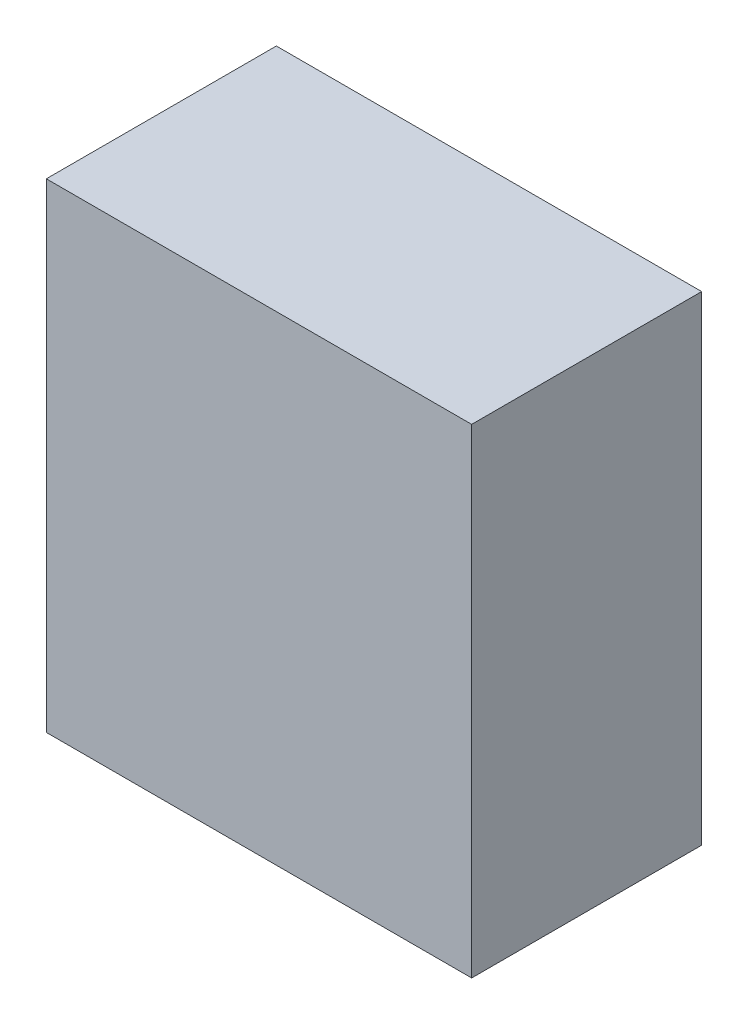
SolidWorks part; units mm, degrees
ref_plane "Front Plane" through (0, 0, 0) normal (0, 0, 1) x (1, 0, 0)
ref_plane "Top Plane" through (0, 0, 0) normal (0, 1, 0) x (1, 0, 0)
ref_plane "Right Plane" through (0, 0, 0) normal (1, 0, 0) x (0, 0, -1)
sketch "Sketch1" plane through (0, 0, 0) normal (0, 0, 1) x (1, 0, 0)
  line L3 (-155.3667, 7.5842) -> (-172.6667, 7.5842)
  line L4 (-155.3667, -14.9158) -> (-155.3667, 7.5842)
  line L5 (-172.6667, -14.9158) -> (-155.3667, -14.9158)
  line L6 (-172.6667, 7.5842) -> (-172.6667, 12.3342)
  line L7 (-172.6667, 12.3342) -> (-144.2806, 12.3342)
  line L8 (-144.2806, 12.3342) -> (-144.2806, -19.6658)
  line L9 (-144.2806, -19.6658) -> (-172.6667, -19.6658)
  line L10 (-172.6667, -19.6658) -> (-172.6667, -14.9158)
extrude "Boss-Extrude1" add sketch "Sketch1" against normal up to surface (12.35 mm away)
sketch "Sketch2" plane through (0, 0, 0) normal (0, 0, 1) x (1, 0, 0)
  line L1 (-144.2806, -19.6658) -> (-172.6667, -19.6658)
  line L2 (-144.2806, -19.6658) -> (-144.2806, 12.3342)
  line L3 (-144.2806, 12.3342) -> (-172.6667, 12.3342)
  line L4 (-172.6667, -19.6658) -> (-172.6667, 12.3342)
extrude "Boss-Extrude2" add sketch "Sketch2" along normal blind 3
